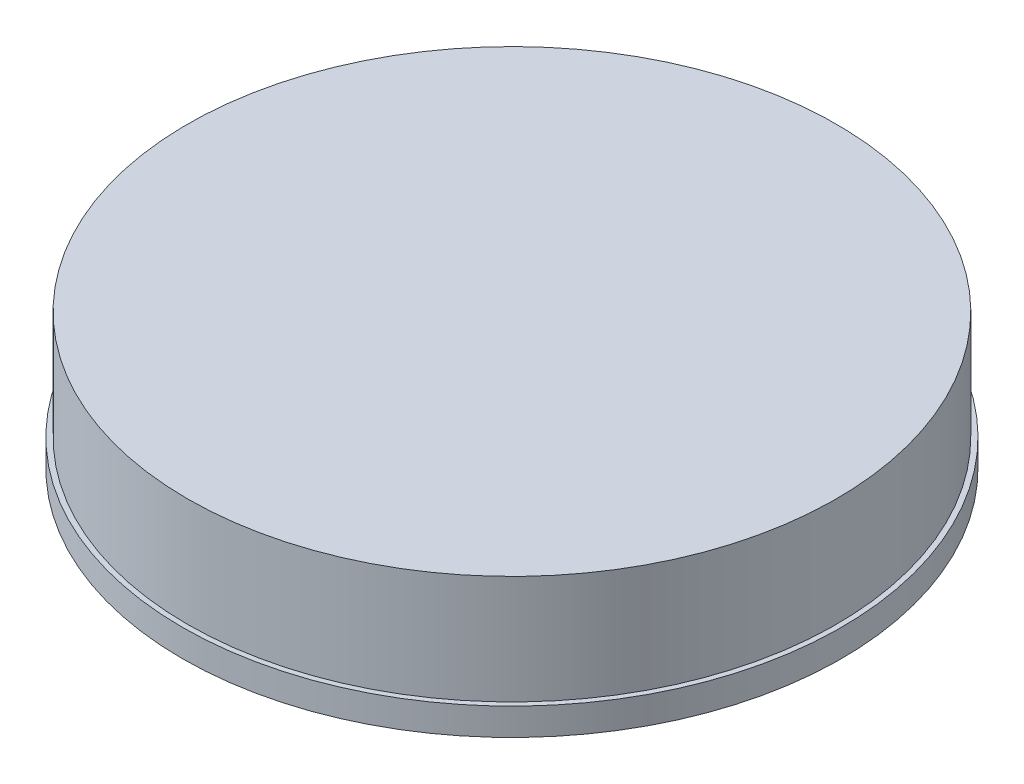
SolidWorks part; units mm, degrees
ref_plane "Front Plane" through (0, 0, 0) normal (0, 0, 1) x (1, 0, 0)
ref_plane "Top Plane" through (0, 0, 0) normal (0, 1, 0) x (1, 0, 0)
ref_plane "Right Plane" through (0, 0, 0) normal (1, 0, 0) x (0, 0, -1)
sketch "Sketch1" plane through (0, 0, 0) normal (0, 1, 0) x (1, 0, 0)
  circle A0 centre (0, 0) radius 9.7
extrude "Boss-Extrude1" add sketch "Sketch1" along normal blind 0.8
sketch "Sketch2" plane through (0, 0.8, 0) normal (0, 1, 0) x (1, 0, 0)
  circle A0 centre (0, 0) radius 9.55
extrude "Boss-Extrude2" add sketch "Sketch2" along normal blind 3.2
sketch "Sketch4" plane through (0, 0, 0) normal (0, -1, 0) x (-1, 0, 0)
  circle A0 centre (0, 0) radius 8.75
extrude "Cut-Extrude2" cut sketch "Sketch4" against normal blind 3.2
